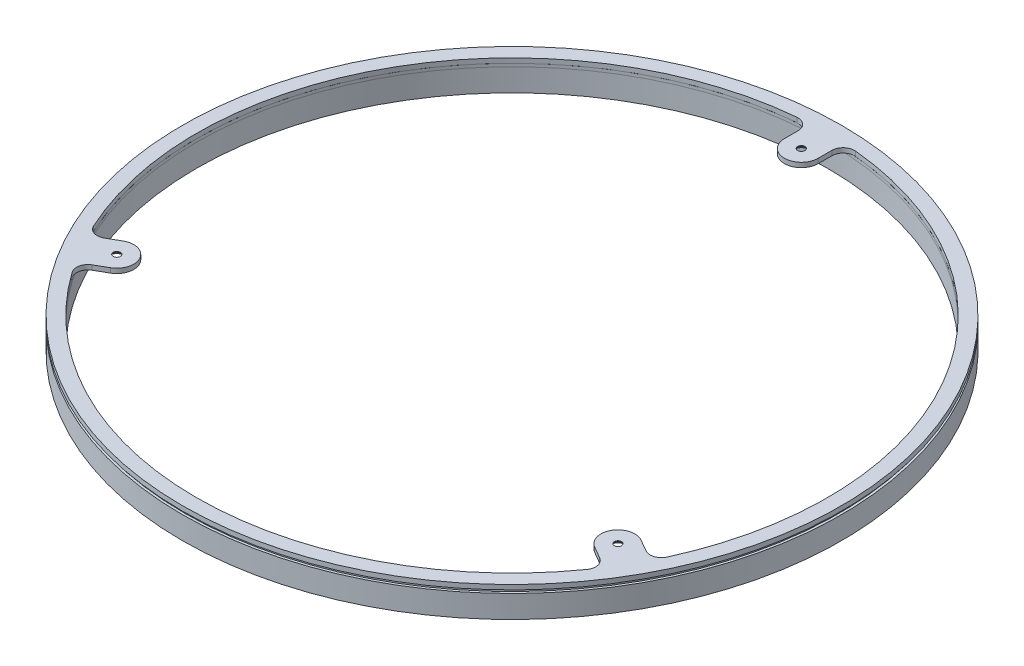
SolidWorks part; units mm, degrees
other "skirt_analogue"
other "foam"
other "dome_ring" parameters "D1"=147.9483, "D2"=256.125, "D3"=35.4447, "D4"=3.5
ref_plane "Front Plane" through (0, 0, 0) normal (0, 0, 1) x (1, 0, 0)
ref_plane "Top Plane" through (0, 0, 0) normal (0, 1, 0) x (1, 0, 0)
ref_plane "Right Plane" through (0, 0, 0) normal (1, 0, 0) x (0, 0, -1)
sketch "Sketch1" plane through (0, 0, 0) normal (0, 1, 0) x (1, 0, 0)
  circle A0 centre (0, 0) radius 145.86
  circle A1 centre (0, 0) radius 139.67
  dimension "D1" = 291.72
  dimension "D2" = 279.34
extrude "Boss-Extrude1" add sketch "Sketch1" along normal blind 2.0746
sketch "Sketch6" plane through (0, 0, 0) normal (0, -1, 0) x (1, 0, 0)
  circle A0 centre (0, 0) radius 139.67 construction
  circle A1 centre (0, 0) radius 139.67
  circle A2 centre (0, 0) radius 144.84
  dimension "D1" = 289.68
extrude "Boss-Extrude3" add sketch "Sketch6" along normal blind 1.3431 separate body
sketch "Sketch7" plane through (0, -1.3431, 0) normal (0, -1, 0) x (1, 0, 0)
  circle A0 centre (0, 0) radius 145.88
  circle A1 centre (0, 0) radius 139.67 construction
  circle A2 centre (0, 0) radius 139.67
  dimension "D1" = 291.76
extrude "Boss-Extrude4" add sketch "Sketch7" along normal blind 10 separate body
sketch "Sketch8" plane through (0, 0, 0) normal (0, 1, 0) x (1, 0, 0)
  line L0 (-7.5, 128.0625) -> (-7.5, 139.4685)
  line L1 (7.5, 128.0625) -> (7.5, 139.4685)
  circle A0 centre (0, 0) radius 139.67 construction
  arc A1 (7.5, 139.4685) -> (-7.5, 139.4685) centre (0, 0) ccw
  circle A2 centre (0, 0) radius 128.0625 construction
  arc A4 (-7.5, 128.0625) -> (7.5, 128.0625) centre (0, 128.0625) ccw
  arc A5 (7.5, 128.0625) -> (-7.5, 128.0625) centre (0, 128.0625) ccw construction
  arc A6 (-7.5, 139.4685) -> (7.5, 139.4685) centre (0, 0) ccw construction
  dimension "D1" = 256.125
  dimension "D3" = 15
extrude "Boss-Extrude5" add sketch "Sketch8" along normal up to surface (2.0746 mm away) up to face at (0, 2.0746, 145.86)
fillet "Fillet1" radius 5 2 edges at (7.5, 1.0373, -139.4685) (-7.5, 1.0373, -139.4685)
sketch "Sketch11" plane through (0, 0, 0) normal (0, -1, 0) x (1, 0, 0)
  arc A0 (7.5, -128.0625) -> (-7.5, -128.0625) centre (0, -128.0625) ccw construction
  point P0 (0, -128.0625)
hole_wizard "CSK for M3 Countersunk Flat Head Screw1" positions "Sketch11" profile "Sketch12" countersink size "M3" standard "DIN" end condition through all
sketch "Sketch12" plane through (0, 0, -128.0625) normal (1, 0, 0) x (0, 0, -1)
  line L0 (0, 0) -> (0, 2.0746)
  line L1 (0, 2.0746) -> (1.6, 2.0746)
  line L2 (1.6, 2.0746) -> (1.6, 1.75)
  line L3 (1.6, 1.75) -> (3.35, 0)
  line L5 (3.35, 0) -> (0, 0)
  line L6 (-1.6, 1.75) -> (-3.35, 0) construction
  line L11 (0, -6.35) -> (0, 107.95) construction
  dimension "Thru Hole Dia." = 3.2
  dimension "Thru Hole Depth" = 2.0746
  dimension "Near C'Sink Dia." = 6.7
  dimension "Near C'Sink Angle" = 90
pattern_circular "CirPattern1" count 3 over 360 about axis through (0, 0, 0) along (0, 1, 0) of "Boss-Extrude5", "Fillet1", "CSK for M3 Countersunk Flat Head Screw1"
equation "\"head_mount_circle_diameter\"= 250mm * 1.0245"
equation "\"D1@Sketch8\"=\"head_mount_circle_diameter\""
